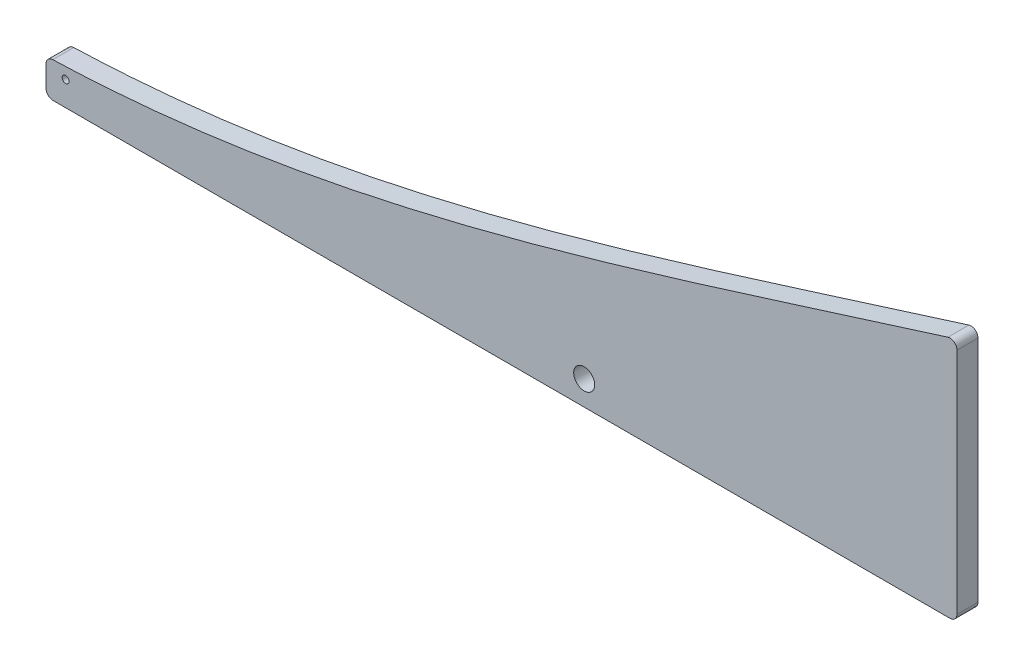
SolidWorks part; units mm, degrees
ref_plane "前视基准面" through (0, 0, 0) normal (0, 0, 1) x (1, 0, 0)
ref_plane "上视基准面" through (0, 0, 0) normal (0, 1, 0) x (1, 0, 0)
ref_plane "右视基准面" through (0, 0, 0) normal (1, 0, 0) x (0, 0, -1)
sketch "草图1" plane through (0, 0, 0) normal (0, 0, 1) x (1, 0, 0)
  line L0 (-34.1617, 0) -> (95.8383, 0)
  line L2 (-34.1617, 0) -> (-34.1617, 5)
  line L6 (95.8383, 35) -> (95.8383, 0)
  circle A0 centre (-31.3617, 3.5) radius 0.5
  circle A1 centre (42.6383, 3.5) radius 1.5
  spline S0 degree 3 poles (-34.1617, 5) (10.6893, 6.2279) (53.6026, 21.9473) (95.8383, 35) knots 0 0 0 0 1 1 1 1
  point P16 (95.8383, 35)
  dimension "D4" = 1
  dimension "D6" = 3
  dimension "D3" = 74
  dimension "D8" = 35
  dimension "D1" = 130
  dimension "D2" = 5
  dimension "D5" = 1.5
  dimension "D7" = 2.8
extrude "凸台-拉伸1" add sketch "草图1" along normal blind 3
fillet "圆角1" radius 1 4 edges at (-34.1617, 0, 1.5) (-34.1617, 5, 1.5) (95.8383, 35, 1.5) (95.8383, 0, 1.5)
